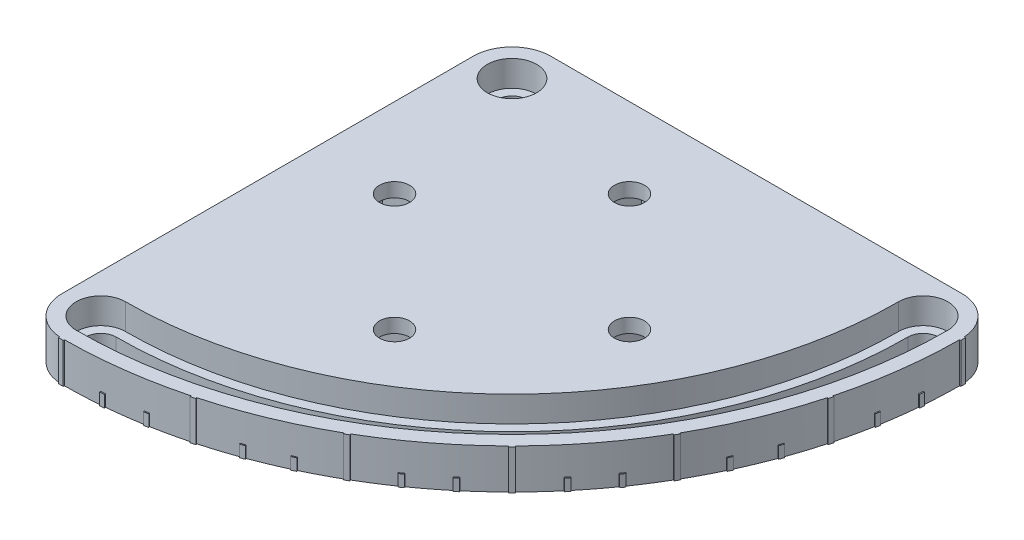
SolidWorks part; units mm, degrees
ref_plane "정면" through (0, 0, 0) normal (0, 0, 1) x (1, 0, 0)
ref_plane "윗면" through (0, 0, 0) normal (0, 1, 0) x (1, 0, 0)
ref_plane "우측면" through (0, 0, 0) normal (1, 0, 0) x (0, 0, -1)
sketch "스케치1" plane through (0, 0, 0) normal (0, 1, 0) x (1, 0, 0)
  line L1 (-8.25, -87.5) -> (-8.25, -22.5)
  line L7 (22.5, 8.25) -> (87.5, 8.25)
  arc A0 (0, -19.25) -> (0, -25.75) centre (0, -22.5) ccw
  arc A1 (25.75, 0) -> (19.25, 0) centre (22.5, 0) ccw
  arc A2 (0, -84.25) -> (0, -90.75) centre (0, -87.5) ccw
  arc A3 (90.75, 0) -> (84.25, 0) centre (87.5, 0) ccw
  arc A4 (0, -25.75) -> (25.75, 0) centre (0, 0) ccw
  arc A5 (0, -19.25) -> (19.25, 0) centre (0, 0) ccw
  arc A6 (0, -84.25) -> (84.25, 0) centre (0, 0) ccw
  arc A7 (0, -90.75) -> (90.75, 0) centre (0, 0) ccw
  circle A8 centre (58.75, -33.75) radius 3.2
  circle A9 centre (33.75, -58.75) radius 3.2
  circle A10 centre (8.75, -33.75) radius 3.2
  circle A11 centre (33.75, -8.75) radius 3.2
  arc A12 (0, -95.75) -> (95.75, 0) centre (0, 0) ccw
  arc A13 (0, -14.25) -> (14.25, 0) centre (0, 0) ccw
  arc A15 (-8.25, -87.5) -> (0, -95.75) centre (0, -87.5) ccw
  arc A16 (95.75, 0) -> (87.5, 8.25) centre (87.5, 0) ccw
  arc A17 (0, -14.25) -> (-8.25, -22.5) centre (0, -22.5) ccw
  arc A18 (22.5, 8.25) -> (14.25, 0) centre (22.5, 0) ccw
  point P0 (33.75, -33.75)
  dimension "D7" = 25
  dimension "D10" = 6.4
  dimension "D3" = 6.5
  dimension "D6" = 25
  dimension "D14" = 5
  dimension "D1" = 33.75
  dimension "D2" = 33.75
  dimension "D4" = 22.5
  dimension "D5" = 87.5
  dimension "D8" = 25
  dimension "D9" = 25
extrude "보스-돌출1" add sketch "스케치1" along normal blind 8.5
sketch "스케치2" plane through (0, 8.5, 0) normal (0, 1, 0) x (1, 0, 0)
  line L0 (0, 0) -> (-0.5027, -95.9987) construction
  line L1 (0, 0) -> (0.5027, -95.9987) construction
  line L2 (0, 0) -> (0, -96) construction
  line L3 (0.4974, -94.9987) -> (0.5027, -95.9987)
  line L4 (-0.4974, -94.9987) -> (-0.5027, -95.9987)
  arc A0 (-0.5027, -95.9987) -> (0.5027, -95.9987) centre (0, 0) ccw
  arc A1 (-0.4974, -94.9987) -> (0.4974, -94.9987) centre (0, 0) ccw
  dimension "D3" = 190
  dimension "D4" = 96
  dimension "D1" = 0.3
  dimension "D2" = 0.3
extrude "보스-돌출2" add sketch "스케치2" against normal up to surface (8.5 mm away) up to face at (12.7675, 0, 12.7675)
pattern_circular "원형 패턴1" count 7 over 90 about axis through (0, 0, 0) along (0, 1, 0) of "보스-돌출2"
sketch "스케치6" plane through (0, 0, 0) normal (0, -1, 0) x (1, 0, 0)
  line L2 (0, 0) -> (95.75, 0) construction
  line L3 (0, 0) -> (95.7487, 0.5013) construction
  line L6 (0, 0) -> (95.7348, -0.5013) construction
  line L7 (95.9987, 0.5027) -> (95.4987, 0.5)
  line L8 (95.9987, -0.5027) -> (95.4987, -0.5)
  arc A1 (95.4987, -0.5) -> (95.4987, 0.5) centre (0, 0) ccw
  arc A2 (95.9987, -0.5027) -> (95.9987, 0.5027) centre (0, 0) ccw
  arc A4 (95.7487, 0.5013) -> (92.6159, 24.2973) centre (0, 0) ccw construction
  arc A5 (87.5, -8.25) -> (95.7348, -0.5013) centre (87.5, 0) ccw construction
  dimension "D1" = 191
  dimension "D2" = 0.3
  dimension "D4" = 96
  dimension "D3" = 0.3
extrude "보스-돌출3" add sketch "스케치6" against normal blind 2.5
pattern_circular "원형 패턴2" count 19 over 90 about axis through (0, 8.5, 0) along (0, -1, 0) of "보스-돌출3"
sketch "스케치7" plane through (0, 0, 0) normal (0, -1, 0) x (1, 0, 0)
  line L0 (0, 0) -> (8.75, 33.75) construction
  line L1 (0, 0) -> (33.75, 58.75) construction
  line L2 (58.75, 33.75) -> (0, 0) construction
  line L3 (0, 0) -> (33.75, 8.75) construction
  line L4 (26.6508, 56.8313) -> (35.6687, 51.6508)
  line L5 (26.6508, 56.8313) -> (31.8313, 65.8492)
  line L6 (35.6687, 51.6508) -> (40.8492, 60.6687)
  line L7 (31.8313, 65.8492) -> (40.8492, 60.6687)
  line L8 (26.6508, 56.8313) -> (40.8492, 60.6687) construction
  line L9 (35.6687, 51.6508) -> (31.8313, 65.8492) construction
  line L10 (51.6508, 35.6687) -> (56.8313, 26.6508)
  line L11 (51.6508, 35.6687) -> (60.6687, 40.8492)
  line L12 (56.8313, 26.6508) -> (65.8492, 31.8313)
  line L13 (60.6687, 40.8492) -> (65.8492, 31.8313)
  line L14 (51.6508, 35.6687) -> (65.8492, 31.8313) construction
  line L15 (56.8313, 26.6508) -> (60.6687, 40.8492) construction
  line L16 (30.0214, 2.4114) -> (40.0886, 5.0214)
  line L17 (30.0214, 2.4114) -> (27.4114, 12.4786)
  line L18 (40.0886, 5.0214) -> (37.4786, 15.0886)
  line L19 (27.4114, 12.4786) -> (37.4786, 15.0886)
  line L20 (30.0214, 2.4114) -> (37.4786, 15.0886) construction
  line L21 (40.0886, 5.0214) -> (27.4114, 12.4786) construction
  line L22 (2.4114, 30.0214) -> (12.4786, 27.4114)
  line L23 (2.4114, 30.0214) -> (5.0214, 40.0886)
  line L24 (12.4786, 27.4114) -> (15.0886, 37.4786)
  line L25 (5.0214, 40.0886) -> (15.0886, 37.4786)
  line L26 (2.4114, 30.0214) -> (15.0886, 37.4786) construction
  line L27 (12.4786, 27.4114) -> (5.0214, 40.0886) construction
  point P5 (33.75, 58.75)
  point P6 (58.75, 33.75)
  point P7 (33.75, 8.75)
  point P12 (8.75, 33.75)
  point P17 (28.6519, 3.45)
  dimension "D1" = 10.4
extrude "컷-돌출1" cut sketch "스케치7" against normal offset from surface (5.5 mm away) 3 up to face at (51.7143, 8.5, 51.7143)
sketch "스케치8" plane through (0, 8.5, 0) normal (0, 1, 0) x (1, 0, 0)
  arc A0 (27.75, 0) -> (17.25, 0) centre (22.5, 0) ccw
  arc A1 (92.75, 0) -> (82.25, 0) centre (87.5, 0) ccw
  arc A2 (0, -17.25) -> (0, -27.75) centre (0, -22.5) ccw
  arc A3 (0, -82.25) -> (0, -92.75) centre (0, -87.5) ccw
  arc A4 (0, -17.25) -> (17.25, 0) centre (0, 0) ccw
  arc A5 (0, -27.75) -> (27.75, 0) centre (0, 0) ccw
  arc A6 (0, -82.25) -> (82.25, 0) centre (0, 0) ccw
  arc A7 (0, -92.75) -> (92.75, 0) centre (0, 0) ccw
  dimension "D1" = 10.5
extrude "컷-돌출2" cut sketch "스케치8" against normal offset from surface (5.5 mm away) 3 up to face at (58.75, 0, 33.75)
sketch "스케치9" plane through (0, 8.5, 0) normal (0, 1, 0) x (1, 0, 0)
  line L0 (-8.25, -22.5) -> (-8.25, 0)
  line L1 (22.5, 8.25) -> (0, 8.25)
  line L2 (-8.25, -22.5) -> (-8.25, -27.75)
  line L3 (27.75, 8.25) -> (22.5, 8.25)
  line L4 (87.5, 8.25) -> (22.5, 8.25) construction
  line L5 (0, -27.75) -> (-8.25, -27.75)
  line L6 (-8.25, -22.5) -> (-8.25, -87.5) construction
  line L7 (27.75, 0) -> (27.75, 8.25)
  arc A0 (0, -27.75) -> (27.75, 0) centre (0, 0) ccw
  arc A1 (0, 8.25) -> (-8.25, 0) centre (0, 0) ccw
  arc A2 (0, -27.75) -> (27.75, 0) centre (0, 0) ccw construction
  point P17 (0, 0)
  point P23 (0, 0)
extrude "보스-돌출4" add sketch "스케치9" against normal up to surface (8.5 mm away) up to face at (58.75, 0, 33.75)
sketch "스케치10" plane through (0, 8.5, 0) normal (0, 1, 0) x (1, 0, 0)
  circle A0 centre (0, 0) radius 3.25
  arc A2 (0, -84.25) -> (0, -90.75) centre (0, -87.5) ccw construction
extrude "컷-돌출3" cut sketch "스케치10" against normal up to surface (8.5 mm away) up to face at (58.75, 0, 33.75)
sketch "스케치11" plane through (0, 8.5, 0) normal (0, 1, 0) x (1, 0, 0)
  circle A0 centre (0, 0) radius 5.25
  arc A1 (0, -82.25) -> (0, -92.75) centre (0, -87.5) ccw construction
extrude "컷-돌출4" cut sketch "스케치11" against normal offset from surface (5.5 mm away) 3 up to face at (0, 0, 3.25)
